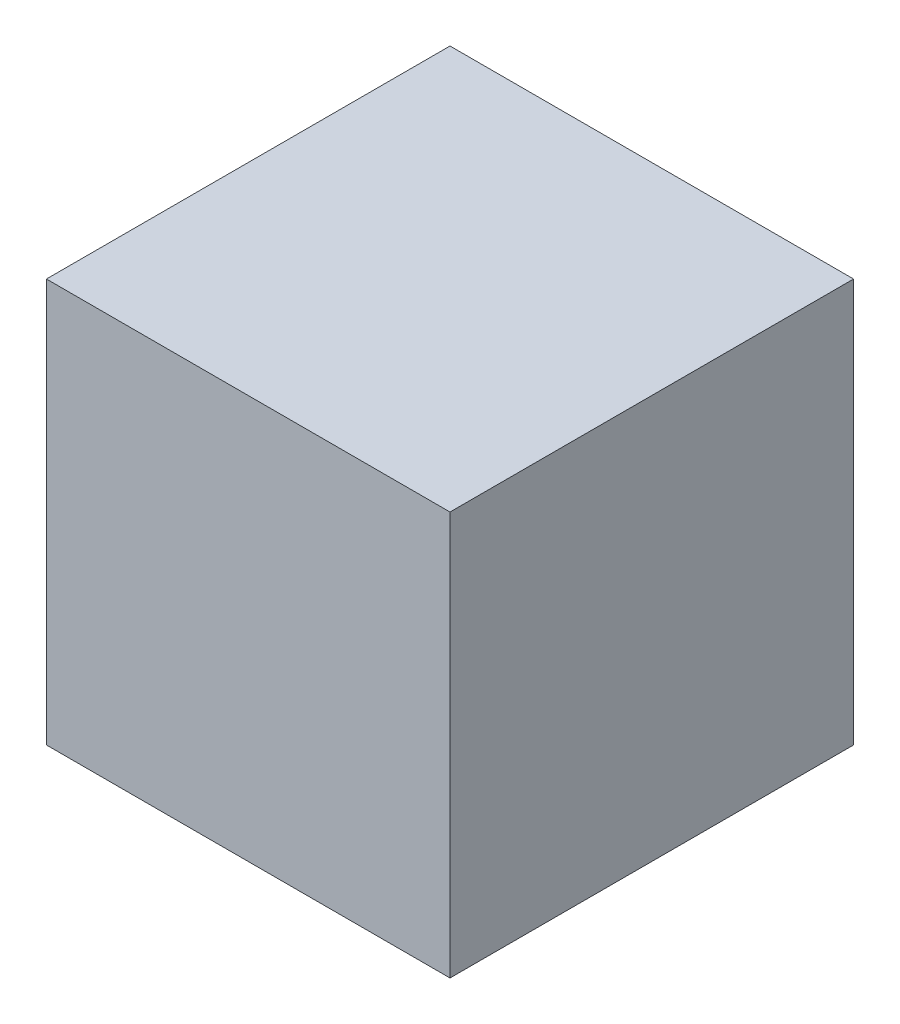
SolidWorks part; units mm, degrees
material "6061 Alloy"
ref_plane "Front Plane" through (0, 0, 0) normal (0, 0, 1) x (1, 0, 0)
ref_plane "Top Plane" through (0, 0, 0) normal (0, 1, 0) x (1, 0, 0)
ref_plane "Right Plane" through (0, 0, 0) normal (1, 0, 0) x (0, 0, -1)
sketch "Sketch1" plane through (0, 0, 0) normal (0, 1, 0) x (1, 0, 0)
  line L1 (-24, -24) -> (24, -24)
  line L2 (-24, -24) -> (-24, 24)
  line L3 (-24, 24) -> (24, 24)
  line L4 (24, -24) -> (24, 24)
  line L5 (-24, -24) -> (24, 24) construction
  line L6 (-24, 24) -> (24, -24) construction
  point P0 (0, 0)
  dimension "D1" = 48
  dimension "D2" = 48
extrude "Boss-Extrude1" add sketch "Sketch1" along normal blind 48
